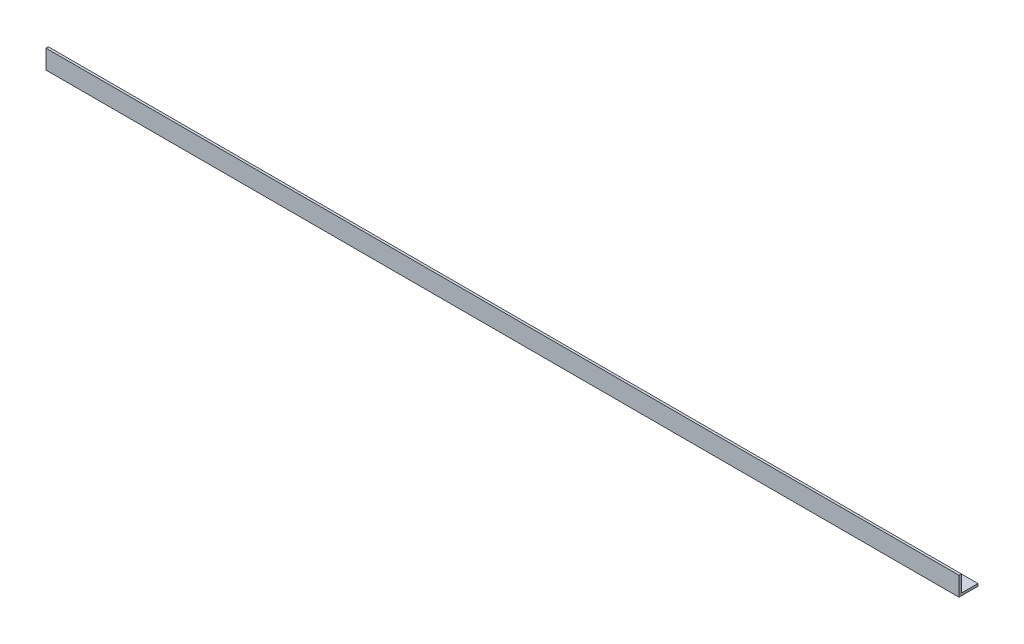
SolidWorks part; units mm, degrees
ref_plane "Front Plane" through (0, 0, 0) normal (0, 0, 1) x (1, 0, 0)
ref_plane "Top Plane" through (0, 0, 0) normal (0, 1, 0) x (1, 0, 0)
ref_plane "Right Plane" through (0, 0, 0) normal (1, 0, 0) x (0, 0, -1)
sketch "Sketch1" plane through (0, 0, 0) normal (1, 0, 0) x (0, 0, -1)
  line L0 (0, 0) -> (0, 25.4)
  line L1 (0, 25.4) -> (3.175, 25.4)
  line L2 (3.175, 25.4) -> (3.175, 3.175)
  line L3 (3.175, 3.175) -> (25.4, 3.175)
  line L4 (25.4, 3.175) -> (25.4, 0)
  line L5 (25.4, 0) -> (0, 0)
  dimension "D1" = 25.4
  dimension "D2" = 3.175
extrude "Boss-Extrude1" add sketch "Sketch1" along normal mid plane 1219.2
